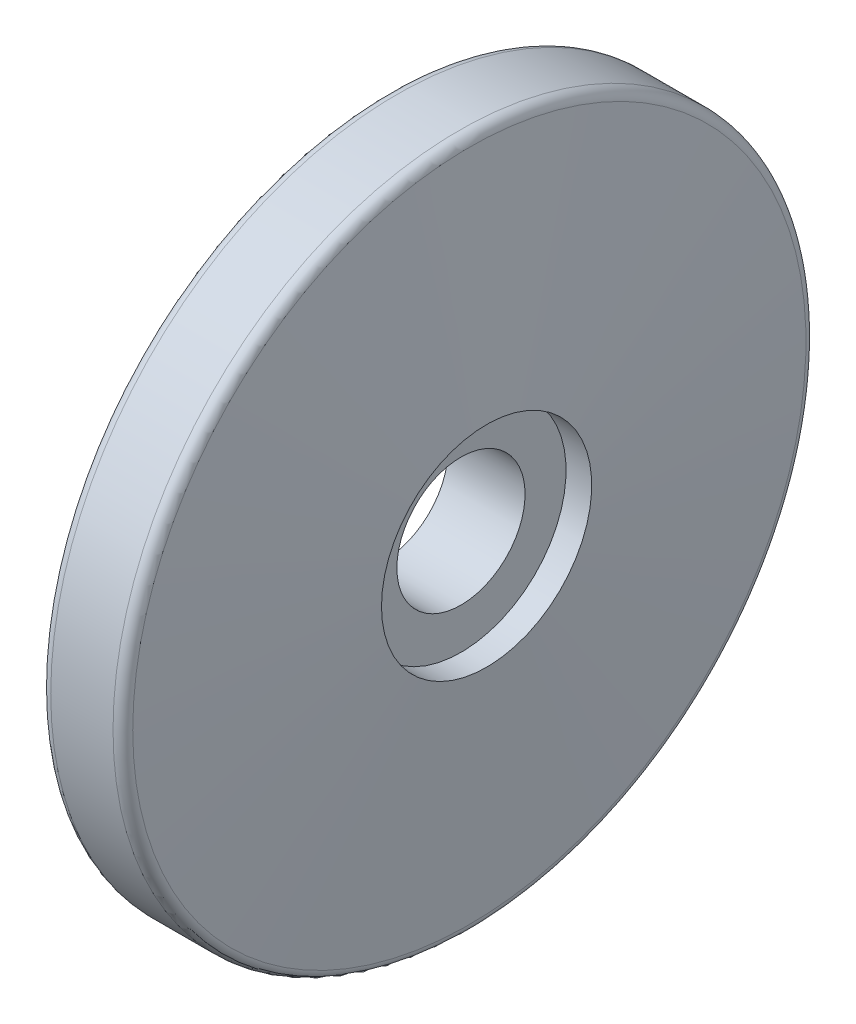
SolidWorks part; units mm, degrees
material "AISI 1020"
ref_plane "Спереди" through (0, 0, 0) normal (0, 0, 1) x (1, 0, 0)
ref_plane "Сверху" through (0, 0, 0) normal (0, 1, 0) x (1, 0, 0)
ref_plane "Справа" through (0, 0, 0) normal (1, 0, 0) x (0, 0, -1)
sketch "Эскиз1" plane through (0, 0, 0) normal (0, 0, 1) x (1, 0, 0)
  line L0 (-643.3327, 0) -> (31523.3015, 0) construction
  line L1 (6.4283, 12.5) -> (-8.5717, 12.5)
  line L2 (-8.5717, 12.5) -> (-8.5717, 26)
  line L3 (-8.5717, 26) -> (-13.0717, 26)
  line L4 (-13.0717, 26) -> (-13.0717, 30)
  line L5 (-13.0717, 30) -> (-8.0717, 30)
  line L6 (-8.0717, 30) -> (-8.0717, 65.5)
  line L7 (-6.0717, 67.5) -> (6.0717, 67.5)
  line L8 (8.0662, 65.6485) -> (11.4283, 20.5)
  line L9 (11.4283, 20.5) -> (6.4283, 20.5)
  line L10 (6.4283, 20.5) -> (6.4283, 12.5)
  arc A0 (6.0717, 67.5) -> (8.0662, 65.6485) centre (6.0717, 65.5) cw
  arc A1 (-8.0717, 65.5) -> (-6.0717, 67.5) centre (-6.0717, 65.5) cw
  point P12 (0, 67.5)
  point P17 (7.9283, 67.5)
  point P20 (-8.0717, 67.5)
  dimension "D11" = 2
  dimension "D1" = 25
  dimension "D2" = 52
  dimension "D3" = 60
  dimension "D4" = 4.5
  dimension "D5" = 19.5
  dimension "D6" = 5
  dimension "D7" = 16
  dimension "D8" = 5
  dimension "D9" = 135
  dimension "D10" = 41
revolve "Повернуть1" add sketch "Эскиз1" angle 360 about L0
